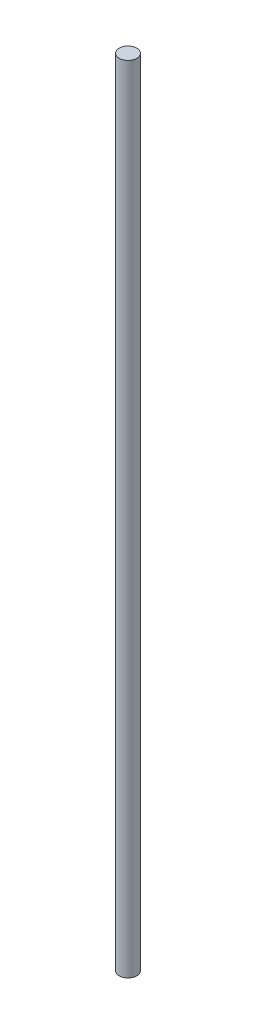
SolidWorks part; units mm, degrees
ref_plane "Alzado" through (0, 0, 0) normal (0, 0, 1) x (1, 0, 0)
ref_plane "Planta" through (0, 0, 0) normal (0, 1, 0) x (1, 0, 0)
ref_plane "Vista lateral" through (0, 0, 0) normal (1, 0, 0) x (0, 0, -1)
sketch "Croquis1" plane through (0, 0, 0) normal (0, 1, 0) x (1, 0, 0)
  circle A0 centre (0, 0) radius 4
  dimension "D1" = 8
extrude "Saliente-Extruir1" add sketch "Croquis1" along normal blind 360
